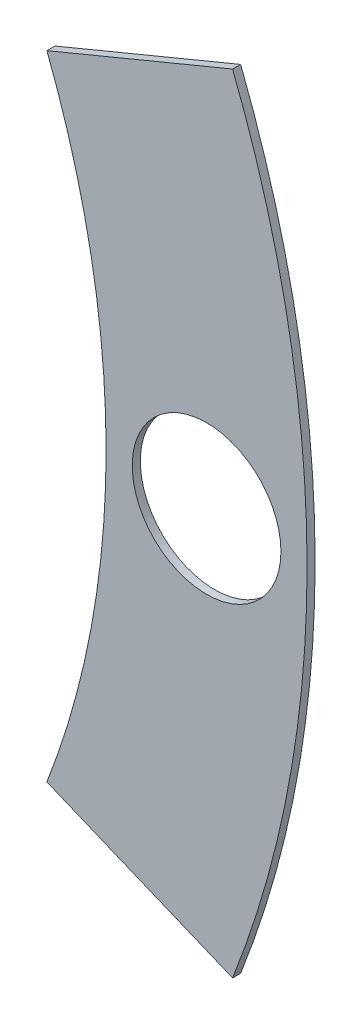
SolidWorks part; units mm, degrees
material "Copper"
ref_plane "Front Plane" through (0, 0, 0) normal (0, 0, 1) x (1, 0, 0)
ref_plane "Top Plane" through (0, 0, 0) normal (0, 1, 0) x (1, 0, 0)
ref_plane "Right Plane" through (0, 0, 0) normal (1, 0, 0) x (0, 0, -1)
sketch "Sketch4" plane through (0, 0, 0) normal (0, 0, 1) x (1, 0, 0)
  circle A0 centre (0, 0) radius 68.072
  dimension "D1" = 136.144
extrude "Boss-Extrude2" add sketch "Sketch4" along normal blind 0.508
sketch "Sketch5" plane through (0, 0, 0.508) normal (0, 0, 1) x (1, 0, 0)
  circle A0 centre (0, 0) radius 55.372
  circle A1 centre (0, 0) radius 68.072 construction
  dimension "D1" = 12.7
extrude "Cut-Extrude5" cut sketch "Sketch5" against normal through all
sketch "Sketch6" plane through (0, 0, 0.508) normal (0, 0, 1) x (1, 0, 0)
  line L0 (0, 0) -> (61.722, 0) construction
  circle A0 centre (61.722, 0) radius 4.699
  circle A1 centre (0, 0) radius 55.372 construction
  dimension "D2" = 9.398
  dimension "D1" = 6.35
extrude "Cut-Extrude6" cut sketch "Sketch6" against normal through all
sketch "Sketch8" plane through (0, 0, 0.508) normal (0, 0, 1) x (1, 0, 0)
  line L0 (0, 0) -> (62.8903, -26.05) construction
  line L1 (0, 0) -> (62.8903, 26.05) construction
  line L2 (51.6296, -20.011) -> (63.3654, -24.8722)
  line L3 (51.6296, 20.011) -> (63.3654, 24.8722)
  line L6 (0, 0) -> (68.072, 0) construction
  circle A0 centre (0, 0) radius 68.072 construction
  arc A1 (63.3654, -24.8722) -> (63.3654, 24.8722) centre (0, 0) ccw
  arc A3 (51.6296, -20.011) -> (51.6296, 20.011) centre (0, 0) ccw
  circle A4 centre (0, 0) radius 55.372 construction
  point P26 (0, 0)
  dimension "D3" = 1.27
  dimension "D4" = 1.27
  dimension "D1" = 22.5
  dimension "D2" = 22.5
  dimension "D5" = 1.27
  dimension "D6" = 1.27
extrude "Cut-Extrude11" cut sketch "Sketch8" against normal through all flip side to cut
